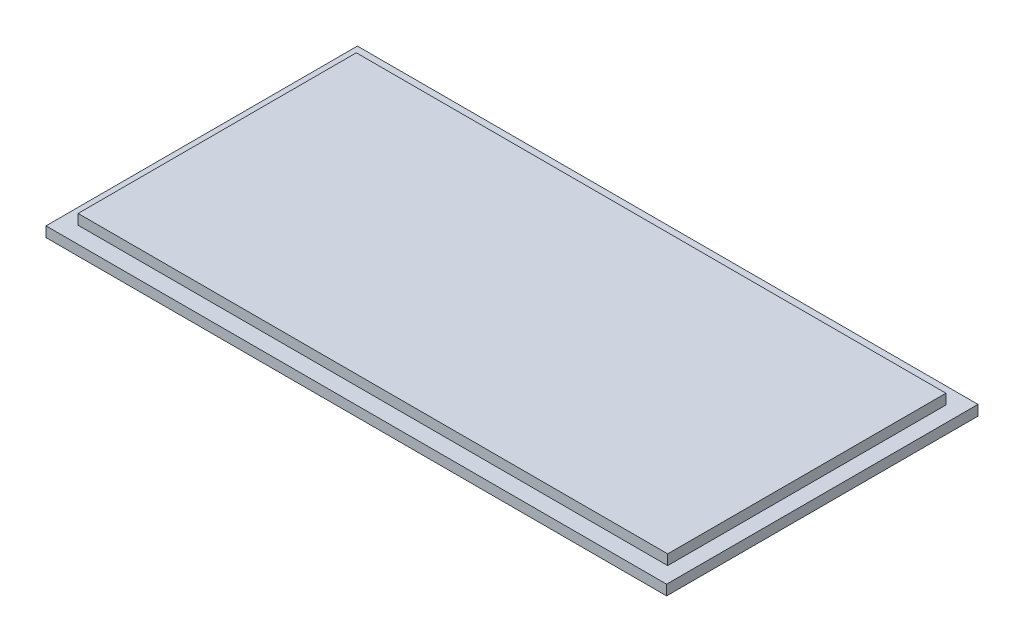
SolidWorks part; units mm, degrees
ref_plane "Front Plane" through (0, 0, 0) normal (0, 0, 1) x (1, 0, 0)
ref_plane "Top Plane" through (0, 0, 0) normal (0, 1, 0) x (1, 0, 0)
ref_plane "Right Plane" through (0, 0, 0) normal (1, 0, 0) x (0, 0, -1)
sketch "Sketch1" plane through (0, 0, 0) normal (0, 1, 0) x (1, 0, 0)
  line L1 (-60.785, 30.5) -> (60.785, 30.5)
  line L2 (-60.785, 30.5) -> (-60.785, -30.5)
  line L3 (-60.785, -30.5) -> (60.785, -30.5)
  line L4 (60.785, 30.5) -> (60.785, -30.5)
  line L5 (-60.785, 30.5) -> (60.785, -30.5) construction
  line L6 (-60.785, -30.5) -> (60.785, 30.5) construction
  point P0 (0, 0)
  dimension "D1" = 121.57
  dimension "D2" = 61
extrude "Boss-Extrude1" add sketch "Sketch1" along normal blind 2
sketch "Sketch2" plane through (0, 2, 0) normal (0, 1, 0) x (1, 0, 0)
  line L1 (-57.75, 27.25) -> (57.75, 27.25)
  line L2 (-57.75, 27.25) -> (-57.75, -27.25)
  line L3 (-57.75, -27.25) -> (57.75, -27.25)
  line L4 (57.75, 27.25) -> (57.75, -27.25)
  line L5 (-57.75, 27.25) -> (57.75, -27.25) construction
  line L6 (-57.75, -27.25) -> (57.75, 27.25) construction
  point P0 (0, 0)
  dimension "D1" = 54.5
  dimension "D2" = 115.5
extrude "Boss-Extrude2" add sketch "Sketch2" along normal blind 2
